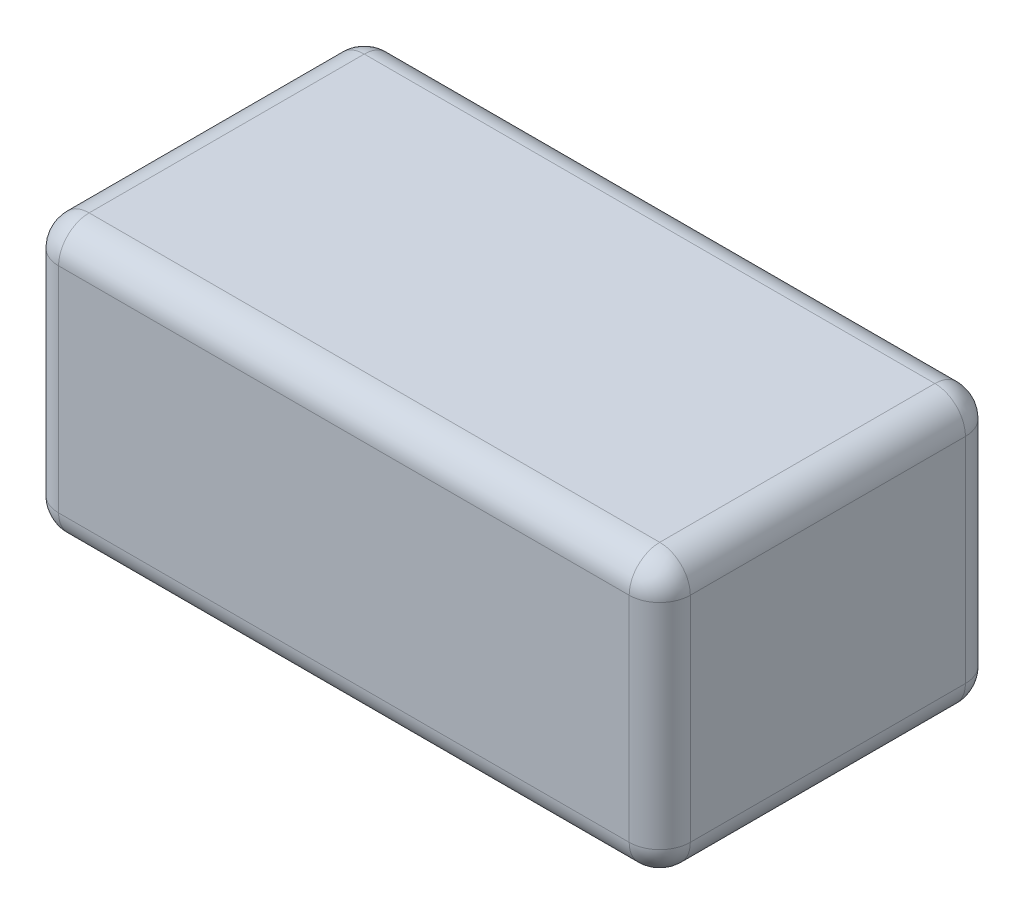
SolidWorks part; units mm, degrees
ref_plane "Front Plane" through (0, 0, 0) normal (0, 0, 1) x (1, 0, 0)
ref_plane "Top Plane" through (0, 0, 0) normal (0, 1, 0) x (1, 0, 0)
ref_plane "Right Plane" through (0, 0, 0) normal (1, 0, 0) x (0, 0, -1)
sketch "Sketch1" plane through (0, 0, 0) normal (1, 0, 0) x (0, 0, -1)
  line L1 (0, 0) -> (-33, 0)
  line L2 (0, 0) -> (0, 27)
  line L3 (0, 27) -> (-33, 27)
  line L4 (-33, 0) -> (-33, 27)
  line L5 (-16.5, 27) -> (-16.5, 0) construction
  line L6 (0, 13.5) -> (-33, 13.5) construction
  point P92 (-16.5, 13.5)
  dimension "D1" = 27
  dimension "D2" = 33
extrude "Boss-Extrude1" add sketch "Sketch1" against normal blind 62
fillet "Fillet1" radius 3 12 edges at (-31, 0, 0) (-62, 0, 16.5) (-31, 0, 33) (0, 0, 16.5) (-31, 27, 33) (-62, 27, 16.5) (-31, 27, 0) (0, 27, 16.5) (-62, 13.5, 0) (-62, 13.5, 33) (0, 13.5, 0) (0, 13.5, 33)
